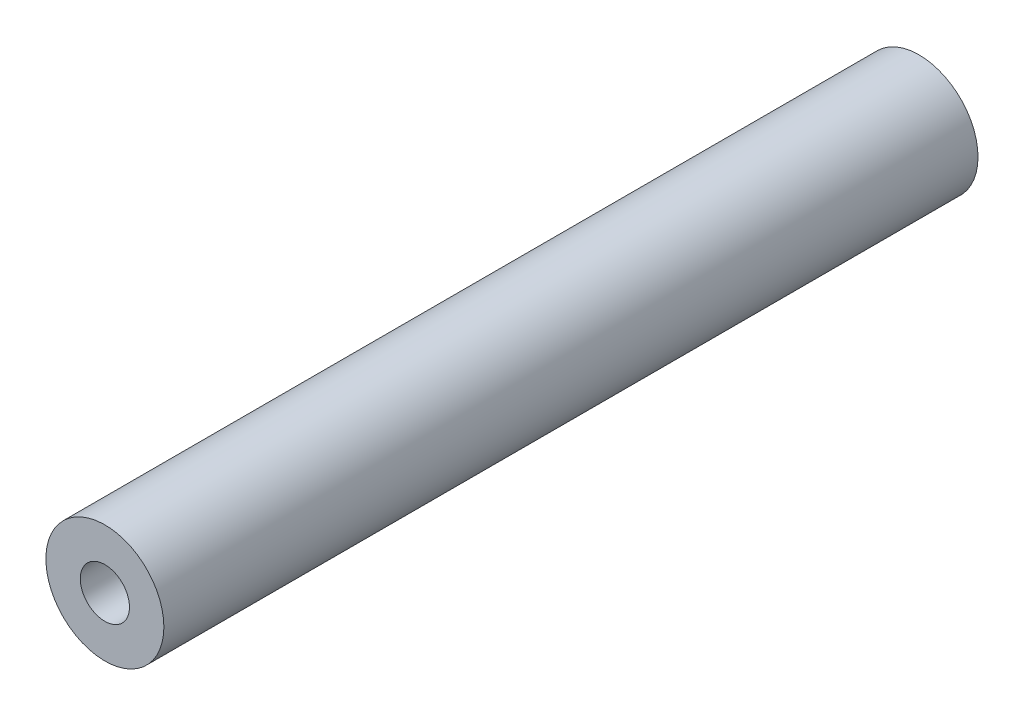
SolidWorks part; units mm, degrees
material "6063-O"
ref_plane "Plano frontal" through (0, 0, 0) normal (0, 0, 1) x (1, 0, 0)
ref_plane "Plano superior" through (0, 0, 0) normal (0, 1, 0) x (1, 0, 0)
ref_plane "Plano direito" through (0, 0, 0) normal (1, 0, 0) x (0, 0, -1)
sketch "Esboço1" plane through (0, 0, 0) normal (0, 0, 1) x (1, 0, 0)
  circle A0 centre (0, 0) radius 3
  dimension "D1" = 6
extrude "Ressalto-extrusão1" add sketch "Esboço1" along normal blind 41.4
sketch "Esboço2" plane through (0, 0, 41.4) normal (0, 0, 1) x (1, 0, 0)
  circle A0 centre (0, 0) radius 1.25
  dimension "D1" = 2.5
extrude "Corte-extrusão1" cut sketch "Esboço2" against normal blind 41.4
